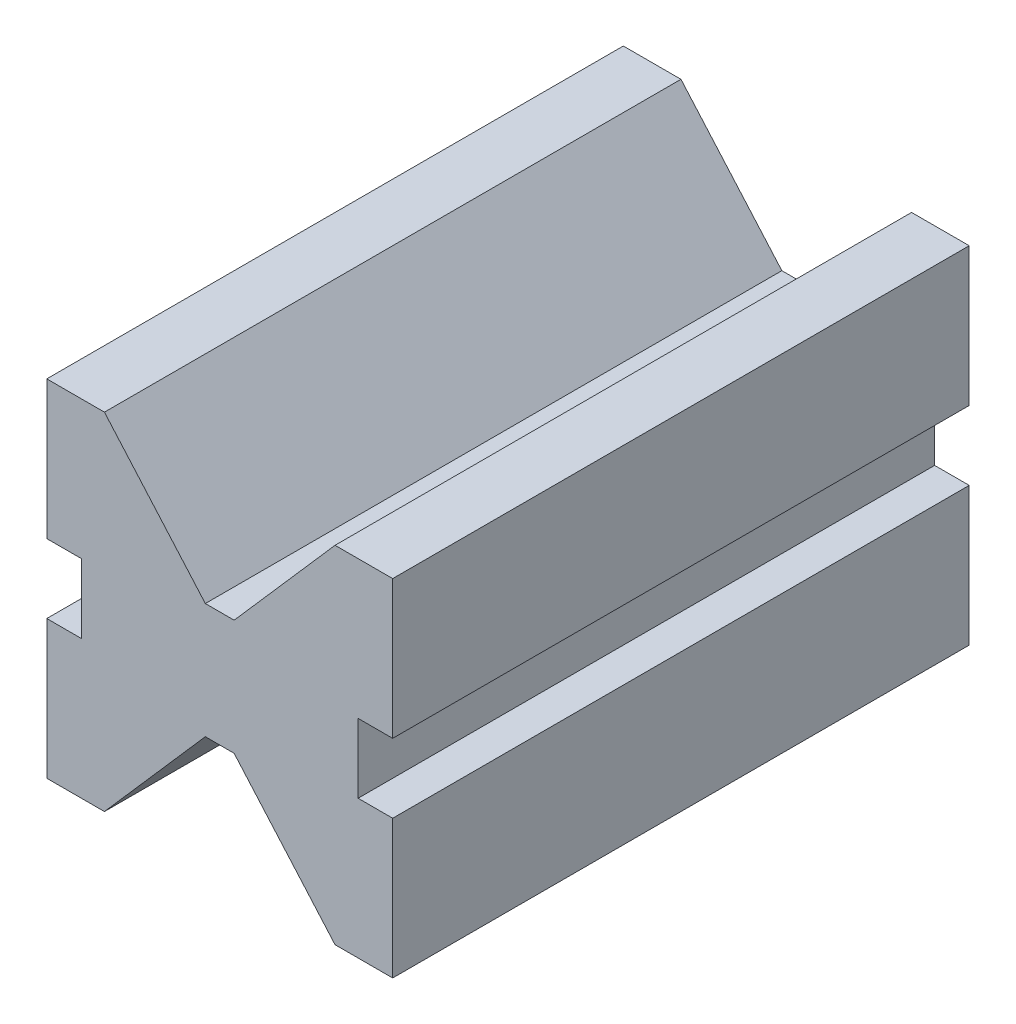
SolidWorks part; units mm, degrees
ref_plane "Ön Düzlem" through (0, 0, 0) normal (0, 0, 1) x (1, 0, 0)
ref_plane "Üst Düzlem" through (0, 0, 0) normal (0, 1, 0) x (1, 0, 0)
ref_plane "Sağ Düzlem" through (0, 0, 0) normal (1, 0, 0) x (0, 0, -1)
sketch "Çizim1" plane through (0, 0, 0) normal (0, 0, 1) x (1, 0, 0)
  line L0 (0, 0) -> (10, 0)
  line L1 (10, 0) -> (27.5, 20)
  line L3 (32.5, 20) -> (50, 0)
  line L4 (50, 0) -> (60, 0)
  line L5 (60, 0) -> (60, 24)
  line L6 (60, 24) -> (54, 24)
  line L7 (54, 24) -> (54, 36)
  line L8 (54, 36) -> (60, 36)
  line L9 (60, 36) -> (60, 60)
  line L10 (60, 60) -> (50, 60)
  line L11 (50, 60) -> (32.5, 40)
  line L13 (27.5, 40) -> (10, 60)
  line L14 (10, 60) -> (0, 60)
  line L15 (0, 60) -> (0, 36)
  line L16 (0, 36) -> (6, 36)
  line L17 (6, 36) -> (6, 24)
  line L18 (6, 24) -> (0, 24)
  line L19 (0, 24) -> (0, 0)
  line L20 (27.5, 20) -> (32.5, 20)
  line L21 (27.5, 40) -> (32.5, 40)
  dimension "D1" = 60
  dimension "D2" = 60
  dimension "D3" = 40
  dimension "D4" = 10
  dimension "D5" = 5
  dimension "D6" = 24
  dimension "D7" = 10
  dimension "D8" = 20
  dimension "D9" = 12
  dimension "D10" = 6
extrude "Yükseklik-Ekstrüzyon1" add sketch "Çizim1" along normal blind 100
